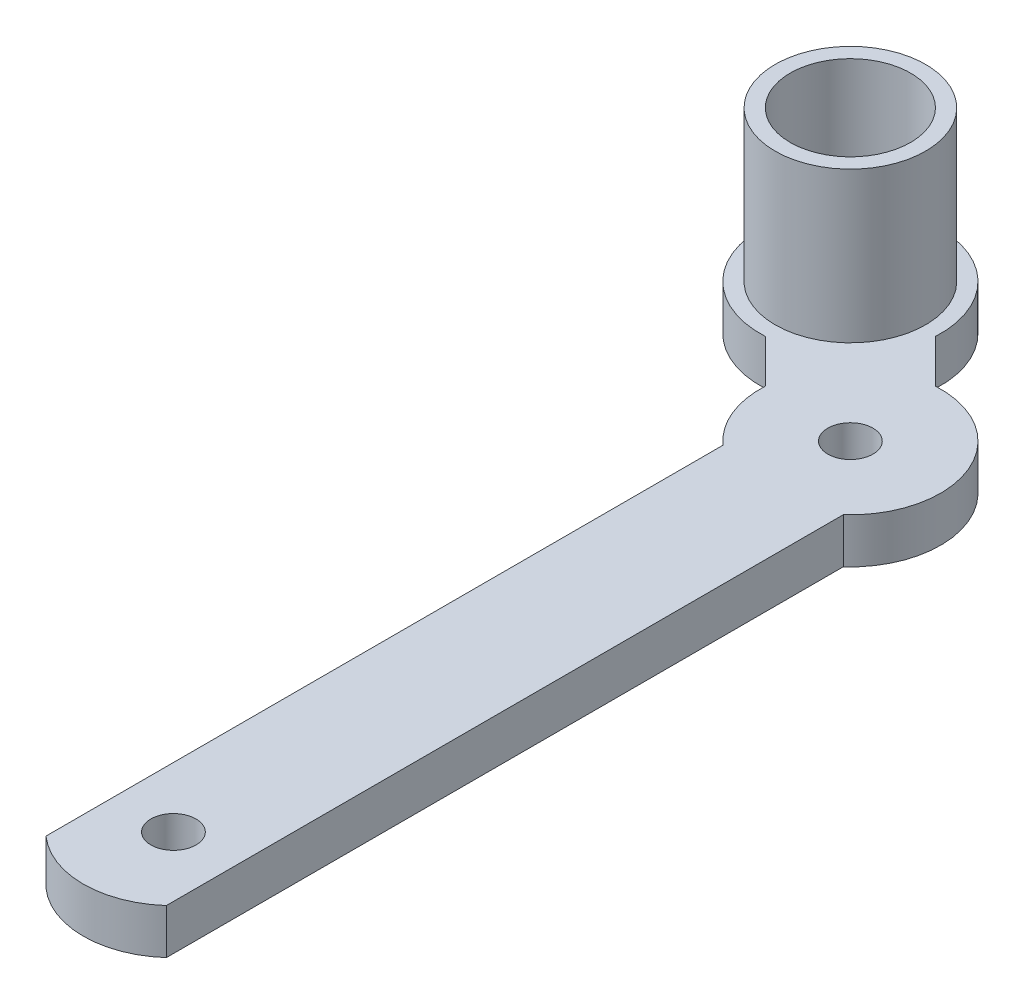
SolidWorks part; units mm, degrees
ref_plane "Plan de face" through (0, 0, 0) normal (0, 0, 1) x (1, 0, 0)
ref_plane "Plan de dessus" through (0, 0, 0) normal (0, 1, 0) x (1, 0, 0)
ref_plane "Plan de droite" through (0, 0, 0) normal (1, 0, 0) x (0, 0, -1)
sketch "Esquisse1" plane through (0, 0, 0) normal (0, 1, 0) x (1, 0, 0)
  line L0 (0, 45) -> (-0.6849, 45)
  line L1 (0, 45) -> (-9.1924, 54.1924) construction
  line L3 (-4, -4.4721) -> (-4, 40.5279)
  line L4 (4, -4.4721) -> (4, 40.5279)
  line L5 (0, 43.5) -> (0, 45) construction
  line L9 (-5.9907, 45.3339) -> (-8.8585, 48.2017)
  line L11 (-0.3339, 50.9907) -> (-3.2017, 53.8585)
  circle A0 centre (0, 0) radius 1.5
  arc A1 (-4, 4.4721) -> (4, 4.4721) centre (0, 0) ccw
  arc A2 (4, 40.5279) -> (-0.3339, 50.9907) centre (0, 45) ccw
  circle A3 centre (0, 45) radius 1.5
  arc A4 (-3.2017, 53.8585) -> (-8.8585, 48.2017) centre (-9.1924, 54.1924) ccw
  circle A5 centre (-9.1924, 54.1924) radius 4
  circle A6 centre (-9.1924, 54.1924) radius 3
  arc A7 (-5.9907, 45.3339) -> (-4, 40.5279) centre (0, 45) ccw
  dimension "D1" = 3
  dimension "D2" = 12
  dimension "D3" = 8
  dimension "D6" = 3
  dimension "D7" = 12
  dimension "D8" = 8
  dimension "D9" = 6
  dimension "D4" = 45
extrude "Boss.-Extru.1" add sketch "Esquisse1" along normal blind 3
sketch "Esquisse2" plane through (0, 3, 0) normal (0, 1, 0) x (1, 0, 0)
  circle A0 centre (-9.1924, 54.1924) radius 4
  circle A1 centre (-9.1924, 54.1924) radius 3
  circle A2 centre (-9.1924, 54.1924) radius 5
  dimension "D1" = 8
  dimension "D2" = 10
extrude "Boss.-Extru.2" add sketch "Esquisse2" along normal blind 10 contours A2 A0
